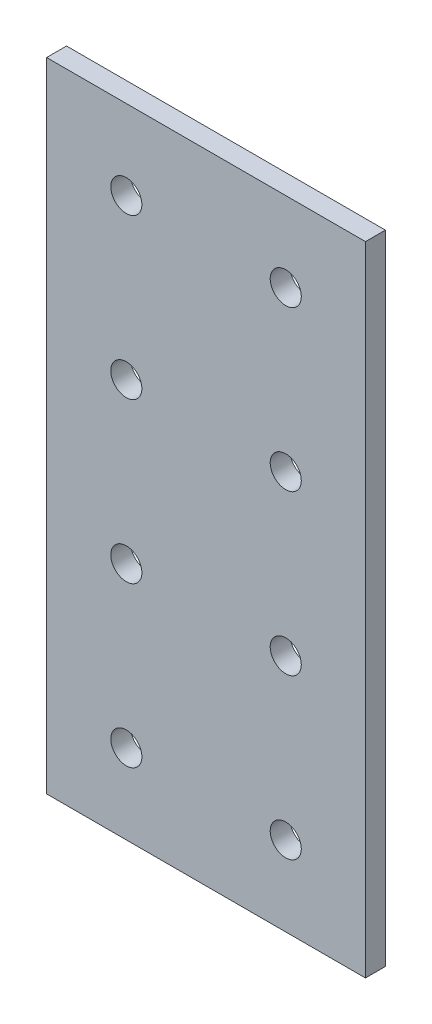
SolidWorks part; units mm, degrees
ref_plane "Front Plane" through (0, 0, 0) normal (0, 0, 1) x (1, 0, 0)
ref_plane "Top Plane" through (0, 0, 0) normal (0, 1, 0) x (1, 0, 0)
ref_plane "Right Plane" through (0, 0, 0) normal (1, 0, 0) x (0, 0, -1)
sketch "Sketch1" plane through (0, 0, 0) normal (0, 0, 1) x (1, 0, 0)
  line L0 (0, 0) -> (25.4, 0)
  line L7 (25.4, 50.8) -> (25.4, 101.6)
  line L8 (25.4, 101.6) -> (-25.4, 101.6)
  line L9 (-25.4, 101.6) -> (-25.4, 50.8)
  line L12 (-25.4, 0) -> (0, 0)
  line L13 (0, 0) -> (0, 101.6) construction
  line L14 (25.4, 50.8) -> (25.4, 0)
  line L15 (-25.4, 50.8) -> (-25.4, 0)
  line L16 (-12.7, 63.5) -> (12.7, 63.5) construction
  line L17 (-12.7, 63.5) -> (-12.7, 88.9) construction
  line L18 (-12.7, 88.9) -> (12.7, 88.9) construction
  line L19 (12.7, 63.5) -> (12.7, 88.9) construction
  line L20 (-12.7, 63.5) -> (12.7, 88.9) construction
  line L21 (-12.7, 88.9) -> (12.7, 63.5) construction
  line L28 (-12.7, 12.7) -> (12.7, 12.7) construction
  line L29 (-12.7, 12.7) -> (-12.7, 38.1) construction
  line L30 (-12.7, 38.1) -> (12.7, 38.1) construction
  line L31 (12.7, 12.7) -> (12.7, 38.1) construction
  line L32 (-12.7, 12.7) -> (12.7, 38.1) construction
  line L33 (-12.7, 38.1) -> (12.7, 12.7) construction
  circle A0 centre (12.7, 88.9) radius 2.4765
  circle A1 centre (-12.7, 88.9) radius 2.4765
  circle A2 centre (-12.7, 63.5) radius 2.4765
  circle A3 centre (12.7, 63.5) radius 2.4765
  circle A4 centre (12.7, 12.7) radius 2.4765
  circle A5 centre (-12.7, 12.7) radius 2.4765
  circle A6 centre (-12.7, 38.1) radius 2.4765
  circle A7 centre (12.7, 38.1) radius 2.4765
  point P3 (0, 0)
  point P5 (0, 76.2)
  point P10 (0, 28.6556)
  point P20 (0, 25.4)
  dimension "D4" = 4.953
  dimension "D1" = 25.4
  dimension "D2" = 50.8
  dimension "D3" = 50.8
  dimension "D5" = 25.4
  dimension "D6" = 25.4
  dimension "D7" = 25.4
extrude "Boss-Extrude1" add sketch "Sketch1" along normal blind 3.175 contours L9 L15 L12 L0 L14 L7 L8
